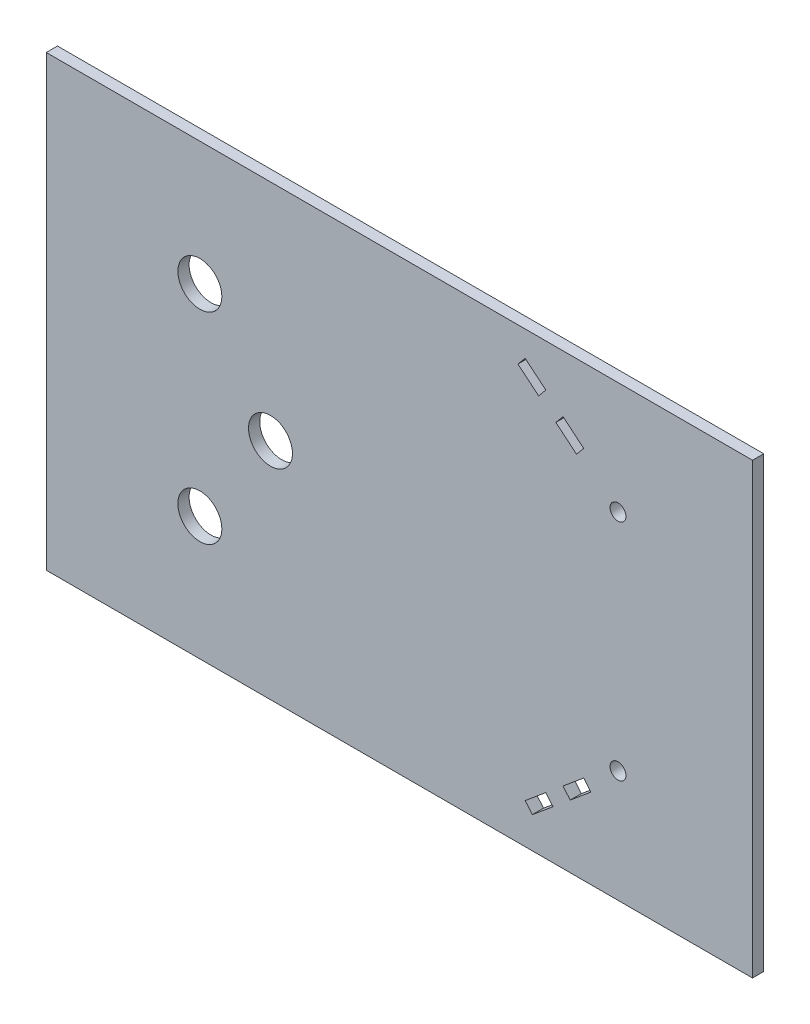
SolidWorks part; units mm, degrees
ref_plane "Front Plane" through (0, 0, 0) normal (0, 0, 1) x (1, 0, 0)
ref_plane "Top Plane" through (0, 0, 0) normal (0, 1, 0) x (1, 0, 0)
ref_plane "Right Plane" through (0, 0, 0) normal (1, 0, 0) x (0, 0, -1)
sketch "Sketch1" plane through (0, 0, 0) normal (0, 0, 1) x (1, 0, 0)
  line L1 (0, 0) -> (400.05, 0)
  line L2 (0, 0) -> (0, 254)
  line L3 (0, 254) -> (400.05, 254)
  line L4 (400.05, 0) -> (400.05, 254)
  dimension "D1" = 400.05
  dimension "D2" = 254
extrude "Boss-Extrude1" add sketch "Sketch1" along normal blind 6.35
sketch "Sketch2" plane through (0, 0, 6.35) normal (0, 0, 1) x (1, 0, 0)
  line L1 (400.05, 254) -> (400.05, 0) construction
  line L2 (0, 247.65) -> (400.05, 247.65) construction
  line L3 (200.025, 0) -> (200.025, 254) construction
  line L4 (0, 0) -> (400.05, 0) construction
  line L5 (400.05, 254) -> (0, 254) construction
  line L6 (295.025, 0) -> (295.025, 254) construction
  line L7 (323.85, 190.5) -> (323.85, 254) construction
  line L8 (323.85, 63.5) -> (323.85, 0) construction
  line L9 (0, 127) -> (400.05, 127) construction
  line L10 (0, 254) -> (0, 0) construction
  line L11 (127, 0) -> (127, 254) construction
  line L14 (87, 0) -> (87, 254) construction
  line L16 (323.85, 0) -> (323.85, 254) construction
  line L18 (271.255, 239.6209) -> (282.9627, 229.8644) construction
  line L19 (292.7191, 221.7341) -> (304.4268, 211.9777) construction
  line L24 (275.3201, 17.7668) -> (287.0278, 27.5232)
  line L25 (275.3201, 17.7668) -> (271.255, 22.645)
  line L26 (287.0278, 27.5232) -> (282.9627, 32.4014)
  line L27 (271.255, 22.645) -> (282.9627, 32.4014)
  line L28 (296.7842, 35.6535) -> (308.4919, 45.41)
  line L29 (296.7842, 35.6535) -> (292.7191, 40.5317)
  line L30 (308.4919, 45.41) -> (304.4268, 50.2882)
  line L31 (292.7191, 40.5317) -> (304.4268, 50.2882)
  line L32 (271.255, 239.6209) -> (282.9627, 229.8644)
  line L33 (271.255, 239.6209) -> (267.1898, 234.7426)
  line L34 (282.9627, 229.8644) -> (278.8975, 224.9862)
  line L35 (267.1898, 234.7426) -> (278.8975, 224.9862)
  line L36 (292.7191, 221.7341) -> (304.4268, 211.9777)
  line L37 (292.7191, 221.7341) -> (288.6539, 216.8559)
  line L38 (304.4268, 211.9777) -> (300.3616, 207.0995)
  line L39 (288.6539, 216.8559) -> (300.3616, 207.0995)
  line L40 (0, 254) -> (0, 0) construction
  line L41 (0, 6.35) -> (400.05, 6.35) construction
  circle A0 centre (323.85, 63.5) radius 4.5
  circle A1 centre (323.85, 190.5) radius 4.5
  circle A2 centre (127, 127) radius 12.446
  circle A3 centre (87, 70) radius 12.446
  circle A4 centre (87, 184) radius 12.446
  dimension "D4" = 6.35
  dimension "D5" = 76.2
  dimension "D21" = 24.892
  dimension "D22" = 24.892
  dimension "D23" = 24.892
  dimension "D1" = 95
  dimension "D2" = 95
  dimension "D3" = 6.35
  dimension "D7" = 40
  dimension "D9" = 6.35
  dimension "D10" = 12.7
  dimension "D11" = 6.35
  dimension "D12" = 15.24
  dimension "D13" = 15.24
  dimension "D14" = 6.35
  dimension "D15" = 6.35
  dimension "D16" = 15.24
  dimension "D17" = 15.24
  dimension "D20" = 12.7
extrude "Cut-Extrude1" cut sketch "Sketch2" against normal blind 6.35
